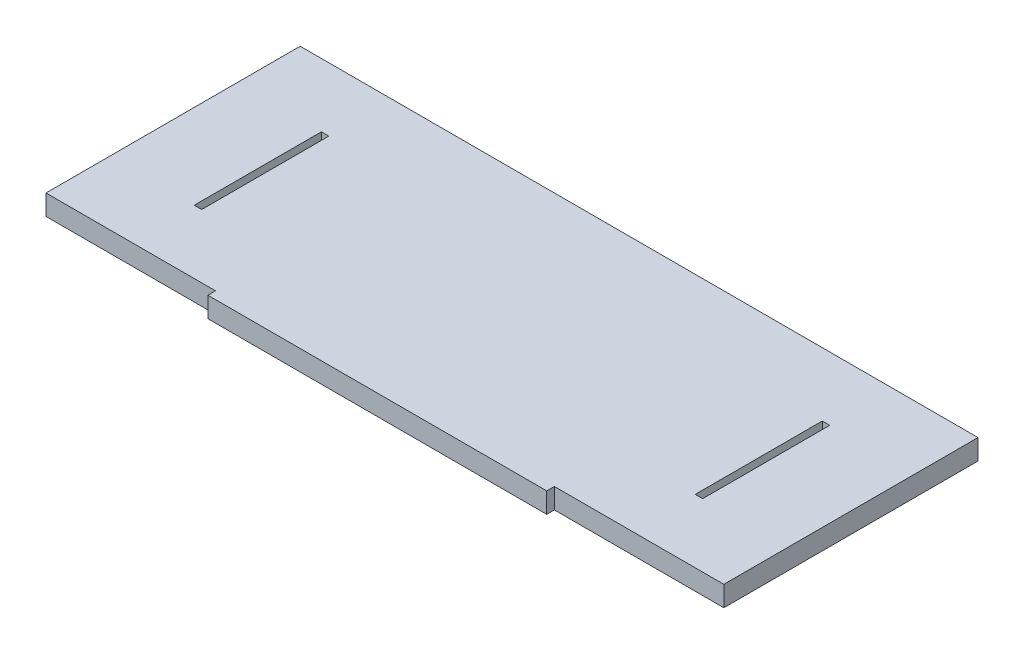
SolidWorks part; units mm, degrees
ref_plane "Front Plane" through (0, 0, 0) normal (0, 0, 1) x (1, 0, 0)
ref_plane "Top Plane" through (0, 0, 0) normal (0, 1, 0) x (1, 0, 0)
ref_plane "Right Plane" through (0, 0, 0) normal (1, 0, 0) x (0, 0, -1)
sketch "Sketch1" plane through (0, 0, 0) normal (0, 1, 0) x (1, 0, 0)
  line L1 (-200, 75) -> (200, 75)
  line L2 (-200, 75) -> (-200, -75)
  line L3 (-200, -75) -> (200, -75)
  line L4 (200, 75) -> (200, -75)
  line L5 (-200, 75) -> (200, -75) construction
  line L6 (-200, -75) -> (200, 75) construction
  line L7 (-100, -70.5) -> (100, -70.5)
  line L8 (-100, -70.5) -> (-100, -79.5)
  line L9 (-100, -79.5) -> (100, -79.5)
  line L10 (100, -70.5) -> (100, -79.5)
  line L11 (-100, -70.5) -> (100, -79.5) construction
  line L12 (-100, -79.5) -> (100, -70.5) construction
  point P0 (0, 0)
  point P5 (0, -75)
  dimension "D1" = 400
  dimension "D2" = 200
  dimension "D3" = 9
  dimension "D4" = 150
extrude "Boss-Extrude1" add sketch "Sketch1" along normal blind 12 contours L7 L10 L3 L4 L1 L2 L8 | L10 L3 L8 L9 | L10 L7 L8 L3
sketch "Sketch3" plane through (0, 12, 0) normal (0, 1, 0) x (1, 0, 0)
  line L0 (-55, 0) -> (55, 0) construction
  line L1 (-150, -37.5) -> (-145.6, -37.5)
  line L2 (-150, -37.5) -> (-150, 37.5)
  line L3 (-150, 37.5) -> (-145.6, 37.5)
  line L4 (-145.6, -37.5) -> (-145.6, 37.5)
  line L5 (-150, -37.5) -> (-145.6, 37.5) construction
  line L6 (-150, 37.5) -> (-145.6, -37.5) construction
  line L7 (-200, 75) -> (-200, -75) construction
  point P0 (-147.8, 0)
  dimension "D1" = 75
  dimension "D2" = 4.4
  dimension "D3" = 50
extrude "Cut-Extrude1" cut sketch "Sketch3" against normal up to surface (12 mm away) contours L2 L3 L4 L1 up to face at (0, 0, 38.625)
mirror "Mirror1" about plane through (0, 0, 0) normal (1, 0, 0) of "Cut-Extrude1"
